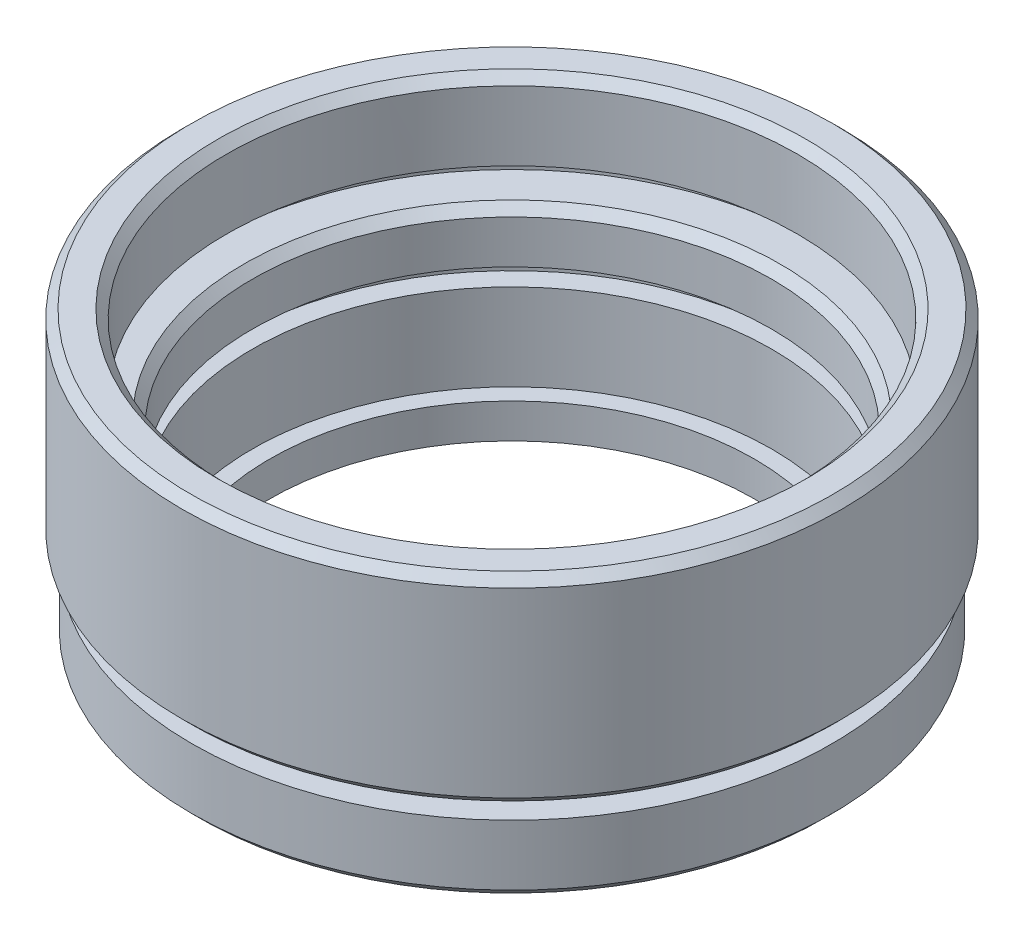
SolidWorks part; units mm, degrees
ref_plane "前视基准面" through (0, 0, 0) normal (0, 0, 1) x (1, 0, 0)
ref_plane "上视基准面" through (0, 0, 0) normal (0, 1, 0) x (1, 0, 0)
ref_plane "右视基准面" through (0, 0, 0) normal (1, 0, 0) x (0, 0, -1)
sketch "草图1" plane through (0, 0, 0) normal (0, 0, 1) x (1, 0, 0)
  line L0 (0, 0) -> (0, 51.3875) construction
  line L1 (14, 0) -> (14, 2)
  line L2 (14, 2) -> (15, 2)
  line L3 (15, 2) -> (15, 7)
  line L4 (15, 7) -> (16.15, 7)
  line L5 (16.15, 7) -> (16.15, 8)
  line L6 (16.15, 8) -> (15, 8)
  line L7 (15, 8) -> (15, 11)
  line L8 (15, 11) -> (17.65, 11)
  line L9 (14, 0) -> (18, 0)
  line L10 (17.65, 11) -> (17.65, 12)
  line L11 (17.65, 12) -> (16.5, 12)
  line L12 (16.5, 12) -> (16.5, 16.5)
  line L13 (16.5, 16.5) -> (18.55, 16.5)
  line L14 (0, 0) -> (5.8539, 0) construction
  line L15 (18.5, 0.5) -> (18.5, 4)
  line L16 (18.5, 4) -> (17, 4)
  line L17 (17, 4) -> (17, 5)
  line L18 (17, 5) -> (18.55, 5)
  line L19 (19.05, 5.5) -> (19.05, 16)
  line L20 (18, 0) -> (18.5, 0.5)
  line L21 (18.55, 5) -> (19.05, 5.5)
  line L22 (19.05, 16) -> (18.55, 16.5)
  point P13 (18.5, 0)
  point P22 (19.05, 5)
  point P24 (19.05, 16.5)
  dimension "D1" = 14
  dimension "D2" = 2
  dimension "D3" = 15
  dimension "D4" = 5
  dimension "D5" = 16.15
  dimension "D6" = 1
  dimension "D7" = 15
  dimension "D8" = 1
  dimension "D9" = 17.65
  dimension "D10" = 5.5
  dimension "D11" = 11.5
  dimension "D12" = 16.5
  dimension "D13" = 18.5
  dimension "D14" = 1
  dimension "D15" = 0.5
  dimension "D16" = 17
  dimension "D17" = 19.05
  dimension "D18" = 0.5
  dimension "D19" = 45
  dimension "D20" = 45
  dimension "D21" = 0.5
  dimension "D22" = 45
  dimension "D23" = 5
revolve "旋转1" add sketch "草图1" angle 360 about L0
cosmetic thread "装饰螺纹线1" parameters "D2"=35
cosmetic thread "装饰螺纹线2" parameters "D2"=35
cosmetic thread "装饰螺纹线3" parameters "D2"=32
chamfer "倒角1" distance 0.5 angle 45 2 edges at (0, 11, -15) (0, 16.5, -16.5)
